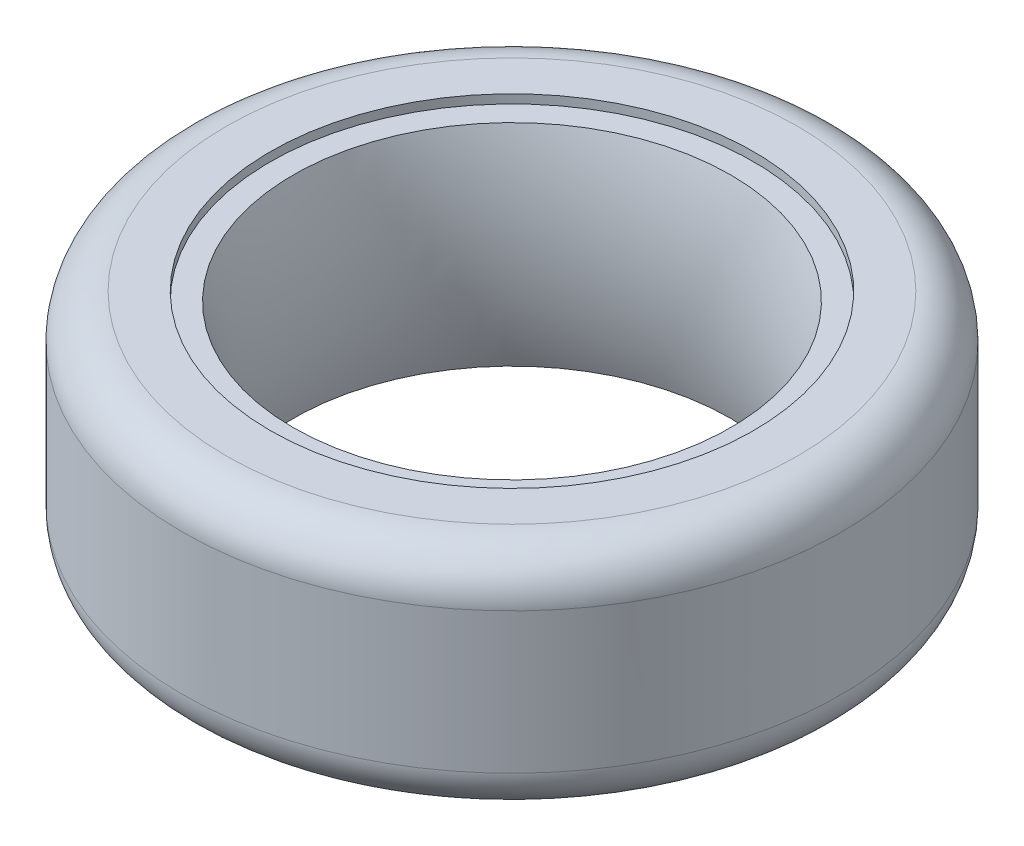
SolidWorks part; units mm, degrees
ref_plane "Front Plane" through (0, 0, 0) normal (0, 0, 1) x (1, 0, 0)
ref_plane "Top Plane" through (0, 0, 0) normal (0, 1, 0) x (1, 0, 0)
ref_plane "Right Plane" through (0, 0, 0) normal (1, 0, 0) x (0, 0, -1)
sketch "Sketch1" plane through (0, 0, 0) normal (0, 0, 1) x (1, 0, 0)
  line L0 (0, -42.8172) -> (0, 42.8172) construction
  line L2 (-27.5, -13) -> (-27.5, -12)
  line L5 (-27.5, -13) -> (-24.8166, -11.7315) construction
  line L6 (-27.5, 13) -> (-24.9, 11.7709) construction
  line L7 (-27.5, 12) -> (-24.9, 12)
  line L8 (-24.9, 12) -> (-24.9, 11.7709)
  line L9 (-27.5, 13) -> (-37.5, 13)
  line L10 (-24.9, -12) -> (-27.5, -12)
  line L11 (-27.5, 12) -> (-27.5, 13)
  line L12 (-37.5, 13) -> (-37.5, -13)
  line L13 (-37.5, -13) -> (-27.5, -13)
  line L14 (0, 39.1439) -> (0, -38.7056) construction
  arc A0 (-24.9, 12) -> (-25.3655, 11.991) centre (-24.9, 0) ccw
  arc A1 (-24.9, 12) -> (-24.9, -12) centre (-63.0576, 0) cw
  point P0 (0, 0)
  dimension "D6" = 40
  dimension "D1" = 26
  dimension "D2" = 27.5
  dimension "D3" = 37.5
  dimension "D4" = 1
  dimension "D5" = 2.6
  dimension "D7" = 1
revolve "Revolve3" add sketch "Sketch1" angle 360 about L14
fillet "Fillet1" radius 5 2 edges at (0, 13, 37.5) (0, -13, 37.5)
